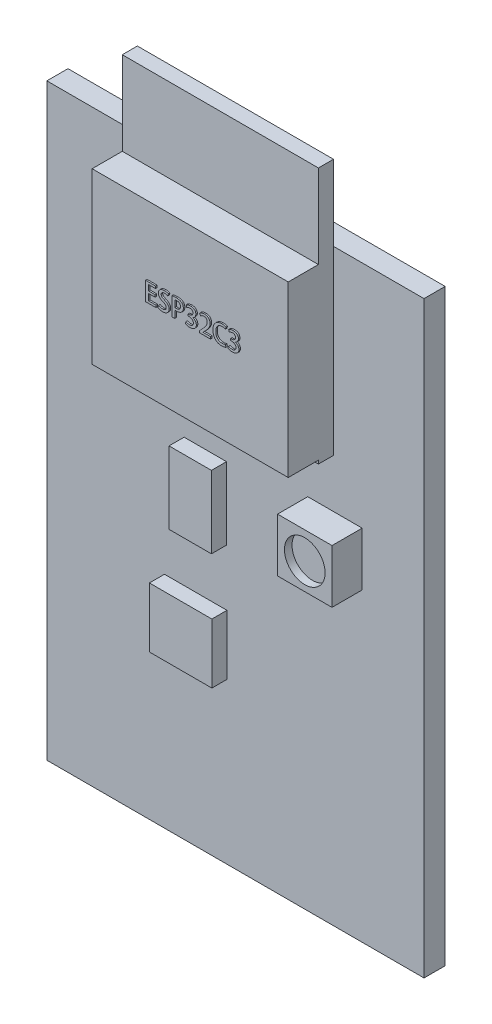
SolidWorks part; units mm, degrees
ref_plane "Plan de face" through (0, 0, 0) normal (0, 0, 1) x (1, 0, 0)
ref_plane "Plan de dessus" through (0, 0, 0) normal (0, 1, 0) x (1, 0, 0)
ref_plane "Plan de droite" through (0, 0, 0) normal (1, 0, 0) x (0, 0, -1)
sketch "Esquisse1" plane through (0, 0, 0) normal (0, 0, 1) x (1, 0, 0)
  line L1 (0, 0) -> (25, 0)
  line L2 (0, 0) -> (0, 39)
  line L3 (0, 39) -> (25, 39)
  line L4 (25, 0) -> (25, 39)
  dimension "D1" = 25
  dimension "D2" = 39
extrude "Boss.-Extru.1" add sketch "Esquisse1" along normal blind 1.4
sketch "Esquisse2" plane through (0, 0, 1.4) normal (0, 0, 1) x (1, 0, 0)
  line L0 (25, 39) -> (25, 44) construction
  line L1 (25, 44) -> (0, 44) construction
  line L2 (12.5, 44) -> (12.5, 39) construction
  line L3 (25, 39) -> (0, 39) construction
  line L4 (12.5, 44) -> (19, 44)
  line L5 (19, 44) -> (19, 27)
  line L6 (12.5, 44) -> (6, 44)
  line L7 (6, 44) -> (6, 27)
  line L8 (6, 27) -> (19, 27)
  dimension "D1" = 5
  dimension "D2" = 17
extrude "Boss.-Extru.2" add sketch "Esquisse2" along normal blind 1
sketch "Esquisse3" plane through (0, 0, 2.4) normal (0, 0, 1) x (1, 0, 0)
  line L0 (6, 44) -> (6, 27) construction
  line L1 (6, 38.4554) -> (19, 38.4554)
  line L2 (6, 38.4554) -> (6, 27.2279)
  line L3 (6, 27.2279) -> (19, 27.2279)
  line L4 (19, 38.4554) -> (19, 27.2279)
  line L5 (19, 27) -> (19, 39) construction
extrude "Boss.-Extru.3" add sketch "Esquisse3" along normal blind 2
sketch "Esquisse4" plane through (0, 0, 1.4) normal (0, 0, 1) x (1, 0, 0)
  line L1 (9.0984, 23.0944) -> (11.9084, 23.0944)
  line L2 (9.0984, 23.0944) -> (9.0984, 18.3027)
  line L3 (9.0984, 18.3027) -> (11.9084, 18.3027)
  line L4 (11.9084, 23.0944) -> (11.9084, 18.3027)
extrude "Boss.-Extru.4" add sketch "Esquisse4" along normal blind 1
sketch "Esquisse5" plane through (0, 0, 1.4) normal (0, 0, 1) x (1, 0, 0)
  line L1 (7.797, 14.5757) -> (11.938, 14.5757)
  line L2 (7.797, 14.5757) -> (7.797, 10.6122)
  line L3 (7.797, 10.6122) -> (11.938, 10.6122)
  line L4 (11.938, 14.5757) -> (11.938, 10.6122)
extrude "Boss.-Extru.5" add sketch "Esquisse5" along normal blind 1
sketch "Esquisse6" plane through (0, 0, 1.4) normal (0, 0, 1) x (1, 0, 0)
  line L1 (17.2918, 23.7747) -> (20.9004, 23.7747)
  line L2 (17.2918, 23.7747) -> (17.2918, 20.2253)
  line L3 (17.2918, 20.2253) -> (20.9004, 20.2253)
  line L4 (20.9004, 23.7747) -> (20.9004, 20.2253)
extrude "Boss.-Extru.6" add sketch "Esquisse6" along normal blind 2
sketch "Esquisse7" plane through (0, 0, 3.4) normal (0, 0, 1) x (1, 0, 0)
  circle A0 centre (19.0961, 21.9749) radius 1.3468
extrude "Enlèv. mat.-Extru.1" cut sketch "Esquisse7" against normal blind 0.5
sketch "Esquisse8" plane through (0, 0, 4.4) normal (0, 0, 1) x (1, 0, 0)
  text T0 "ESP32C3" font "@Adobe Heiti Std R" height in points 4
extrude "Boss.-Extru.7" add sketch "Esquisse8" along normal blind 0.1
